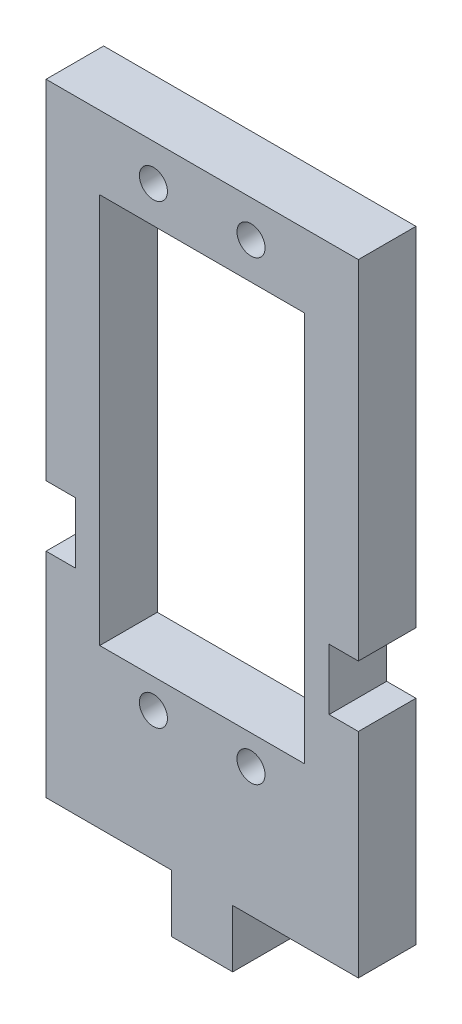
SolidWorks part; units mm, degrees
material "Acrylic (Medium-high impact)"
ref_plane "Front Plane" through (0, 0, 0) normal (0, 0, 1) x (1, 0, 0)
ref_plane "Top Plane" through (0, 0, 0) normal (0, 1, 0) x (1, 0, 0)
ref_plane "Right Plane" through (0, 0, 0) normal (1, 0, 0) x (0, 0, -1)
sketch "Sketch1" plane through (0, 0, 0) normal (0, 0, 1) x (1, 0, 0)
  line L0 (0, 0) -> (0, 64.77) construction
  line L1 (-3.175, -5.9944) -> (3.175, -5.9944)
  line L2 (16.256, 0) -> (16.256, 22.225)
  line L3 (16.256, 64.77) -> (-16.256, 64.77)
  line L4 (-10.668, 16.51) -> (10.668, 16.51)
  line L5 (10.668, 16.51) -> (10.668, 57.15)
  line L6 (10.668, 57.15) -> (-10.668, 57.15)
  line L7 (-10.668, 16.51) -> (-10.668, 57.15)
  line L8 (-16.256, 0) -> (-16.256, 22.225)
  line L9 (16.256, 28.575) -> (13.208, 28.575)
  line L10 (13.208, 28.575) -> (13.208, 22.225)
  line L11 (13.208, 22.225) -> (16.256, 22.225)
  line L12 (16.256, 28.575) -> (16.256, 64.77)
  line L13 (-13.208, 22.225) -> (-16.256, 22.225)
  line L14 (-13.208, 28.575) -> (-13.208, 22.225)
  line L15 (-16.256, 28.575) -> (-13.208, 28.575)
  line L16 (-16.256, 28.575) -> (-16.256, 64.77)
  line L17 (3.175, -5.9944) -> (3.175, 0)
  line L18 (3.175, 0) -> (16.256, 0)
  line L19 (-3.175, 0) -> (-16.256, 0)
  line L20 (-3.175, -5.9944) -> (-3.175, 0)
  circle A0 centre (5.08, 60.96) radius 1.4605
  circle A1 centre (5.08, 13.462) radius 1.4605
  circle A2 centre (-5.08, 13.462) radius 1.4605
  circle A3 centre (-5.08, 60.96) radius 1.4605
  point P10 (0, 57.15)
  point P11 (0, 16.51)
  point P34 (0, -5.9944)
  dimension "D9" = 3.048
  dimension "D6" = 2.921
  dimension "D1" = 16.256
  dimension "D2" = 64.77
  dimension "D3" = 10.668
  dimension "D4" = 40.64
  dimension "D5" = 7.62
  dimension "D7" = 3.81
  dimension "D8" = 5.08
  dimension "D10" = 3.175
  dimension "D11" = 6.35
  dimension "D12" = 3.048
  dimension "D13" = 5.9944
  dimension "D14" = 13.081
  dimension "D15" = 28.575
extrude "Boss-Extrude1" add sketch "Sketch1" along normal blind 5.9944
